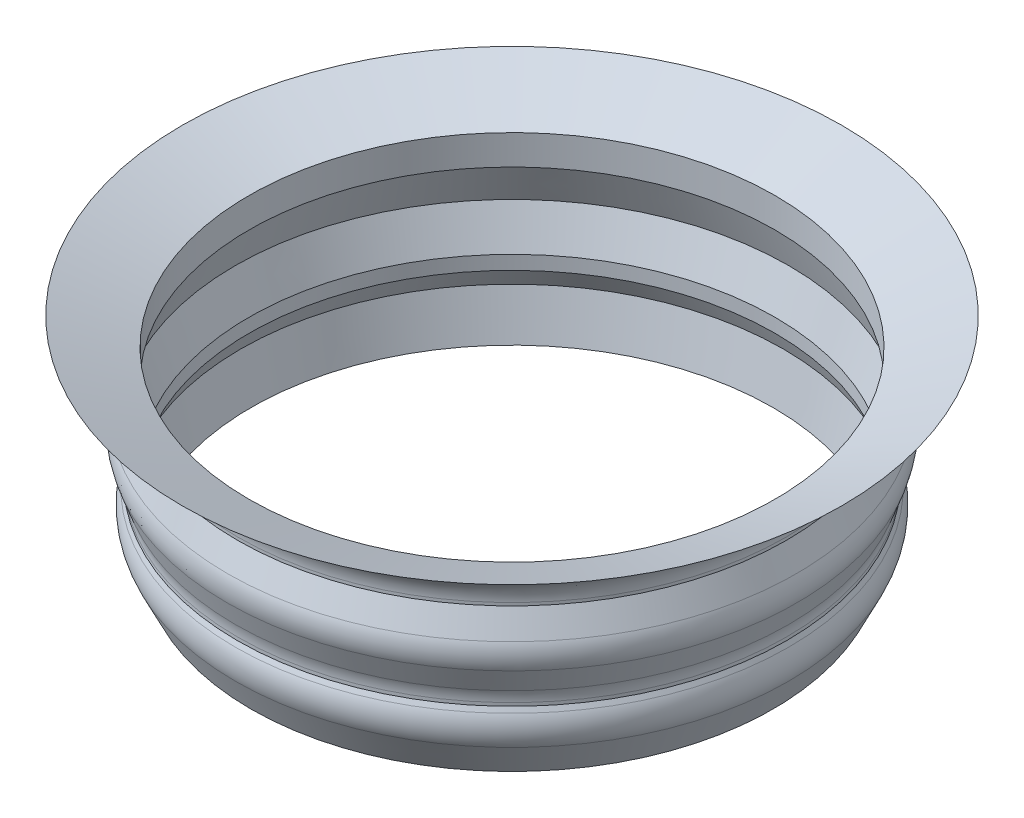
SolidWorks part; units mm, degrees
material "Hexcel AS4C (3000 Filaments)"
ref_plane "Front Plane" through (0, 0, 0) normal (0, 0, 1) x (1, 0, 0)
ref_plane "Top Plane" through (0, 0, 0) normal (0, 1, 0) x (1, 0, 0)
ref_plane "Right Plane" through (0, 0, 0) normal (1, 0, 0) x (0, 0, -1)
sketch "Sketch2" plane through (0, 0, 0) normal (0, 0, 1) x (1, 0, 0)
  line L0 (-73.025, 72.7333) -> (-49.8355, 72.7333) construction
  line L1 (-58.2676, 43.277) -> (-58.2676, 40.2036)
  line L2 (-73.025, 72.7333) -> (-58.2676, 66.6317)
  line L4 (-58.2676, 43.277) -> (-61.3156, 51.6513)
  line L5 (-61.3156, 51.6513) -> (-58.2676, 60.0256)
  line L6 (-58.2676, 60.0256) -> (-58.2676, 66.6317)
  line L7 (-60.129, 36.2394) -> (-57.8313, 26.1638)
  line L9 (-58.2676, 40.2036) -> (-60.129, 36.2394)
  line L10 (0, 0) -> (0, 81.3799) construction
  line L11 (-73.025, 72.7333) -> (-60.8076, 64.8218)
  line L12 (-60.8076, 64.8218) -> (-60.8076, 60.0256)
  line L13 (-60.8076, 60.0256) -> (-64.1379, 51.979)
  line L14 (-64.1379, 51.979) -> (-60.8076, 42.8291)
  line L15 (-60.8076, 42.8291) -> (-60.8076, 40.7702)
  line L16 (-60.8076, 40.7702) -> (-62.829, 36.4653)
  line L17 (-62.829, 36.4653) -> (-57.8313, 26.1638)
  point P8 (-59.7916, 55.8384)
  dimension "D1" = 20
  dimension "D2" = 20
  dimension "D3" = 2.54
  dimension "D4" = 3.0734
  dimension "D5" = 61.3156
  dimension "D6" = 2.54
  dimension "D7" = 2.54
  dimension "D8" = 2.54
  dimension "D9" = 2.54
  dimension "D10" = 73.025
revolve "Revolve1" add sketch "Sketch2" angle 360 about L10
fillet "Fillet1" radius 7.62 4 edges at (0, 42.8291, -60.8076) (0, 64.8218, -60.8076) (0, 36.4653, -62.829) (0, 51.979, -64.1379)
